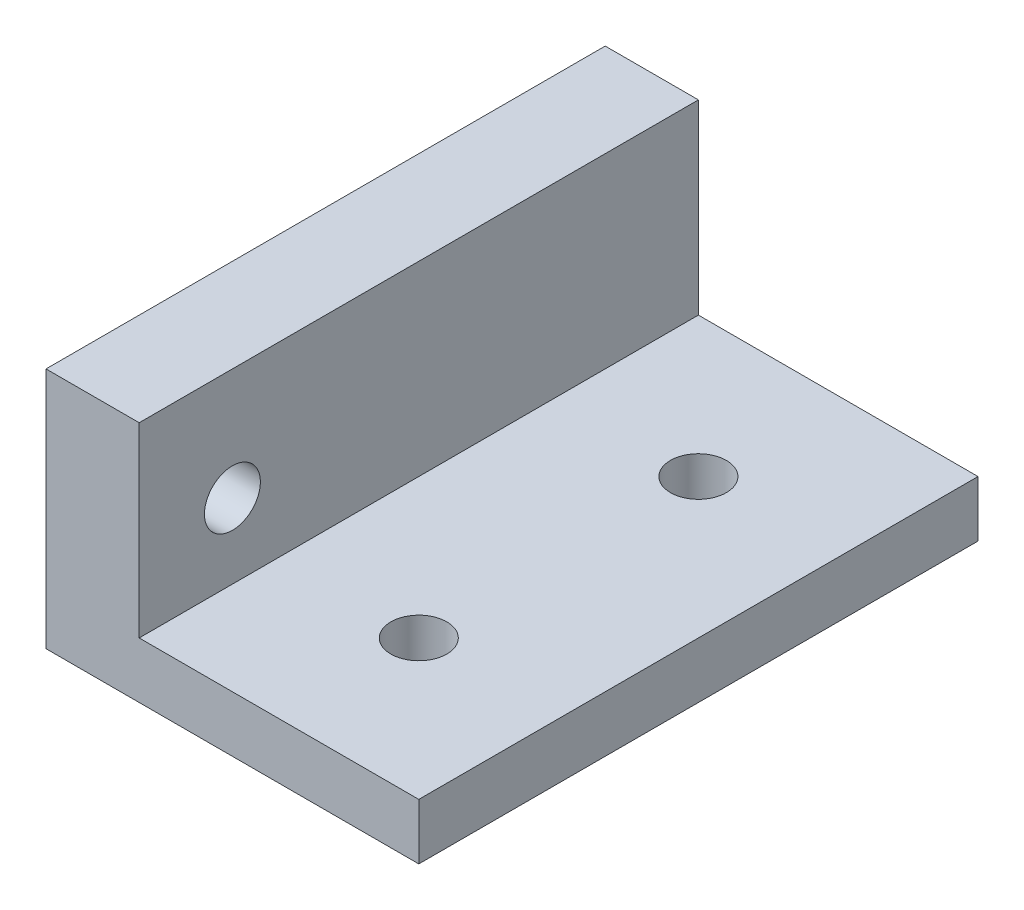
SolidWorks part; units mm, degrees
ref_plane "Front Plane" through (0, 0, 0) normal (0, 0, 1) x (1, 0, 0)
ref_plane "Top Plane" through (0, 0, 0) normal (0, 1, 0) x (1, 0, 0)
ref_plane "Right Plane" through (0, 0, 0) normal (1, 0, 0) x (0, 0, -1)
sketch "Sketch1" plane through (0, 0, 0) normal (0, 1, 0) x (1, 0, 0)
  line L1 (-10, 15) -> (10, 15)
  line L2 (-10, 15) -> (-10, -15)
  line L3 (-10, -15) -> (10, -15)
  line L4 (10, 15) -> (10, -15)
  line L5 (-10, 15) -> (10, -15) construction
  line L6 (-10, -15) -> (10, 15) construction
  point P0 (0, 0)
  dimension "D1" = 20
  dimension "D2" = 30
extrude "Boss-Extrude1" add sketch "Sketch1" along normal blind 3
sketch "Sketch2" plane through (0, 3, 0) normal (0, 1, 0) x (1, 0, 0)
  line L0 (-10, -15) -> (10, -15) construction
  line L1 (-10, 15) -> (-5, 15)
  line L2 (-10, 15) -> (-10, -15)
  line L3 (-10, -15) -> (-5, -15)
  line L4 (-5, 15) -> (-5, -15)
  dimension "D1" = 5
extrude "Boss-Extrude2" add sketch "Sketch2" along normal blind 10
sketch "Sketch3" plane through (-10, 0, 0) normal (-1, 0, 0) x (0, 0, 1)
  line L0 (-15, 7) -> (15, 7) construction
  line L1 (-15, 13) -> (-15, 0) construction
  line L2 (15, 13) -> (15, 0) construction
  line L4 (-15, 0) -> (15, 0) construction
  circle A0 centre (10, 7) radius 1.5
  dimension "D2" = 5
  dimension "D3" = 3
  dimension "D1" = 7
extrude "Cut-Extrude1" cut sketch "Sketch3" against normal blind 10
sketch "Sketch4" plane through (0, 3, 0) normal (0, 1, 0) x (1, 0, 0)
  line L1 (-5, -15) -> (10, -15) construction
  line L2 (10, 15) -> (-5, 15) construction
  line L3 (10, -15) -> (10, 15) construction
  circle A0 centre (2.5, -7.5) radius 1.5
  circle A1 centre (2.5, 7.5) radius 1.5
  dimension "D1" = 3
  dimension "D2" = 3
  dimension "D3" = 7.5
  dimension "D4" = 7.5
  dimension "D5" = 7.5
  dimension "D6" = 7.5
extrude "Cut-Extrude2" cut sketch "Sketch4" against normal through all
